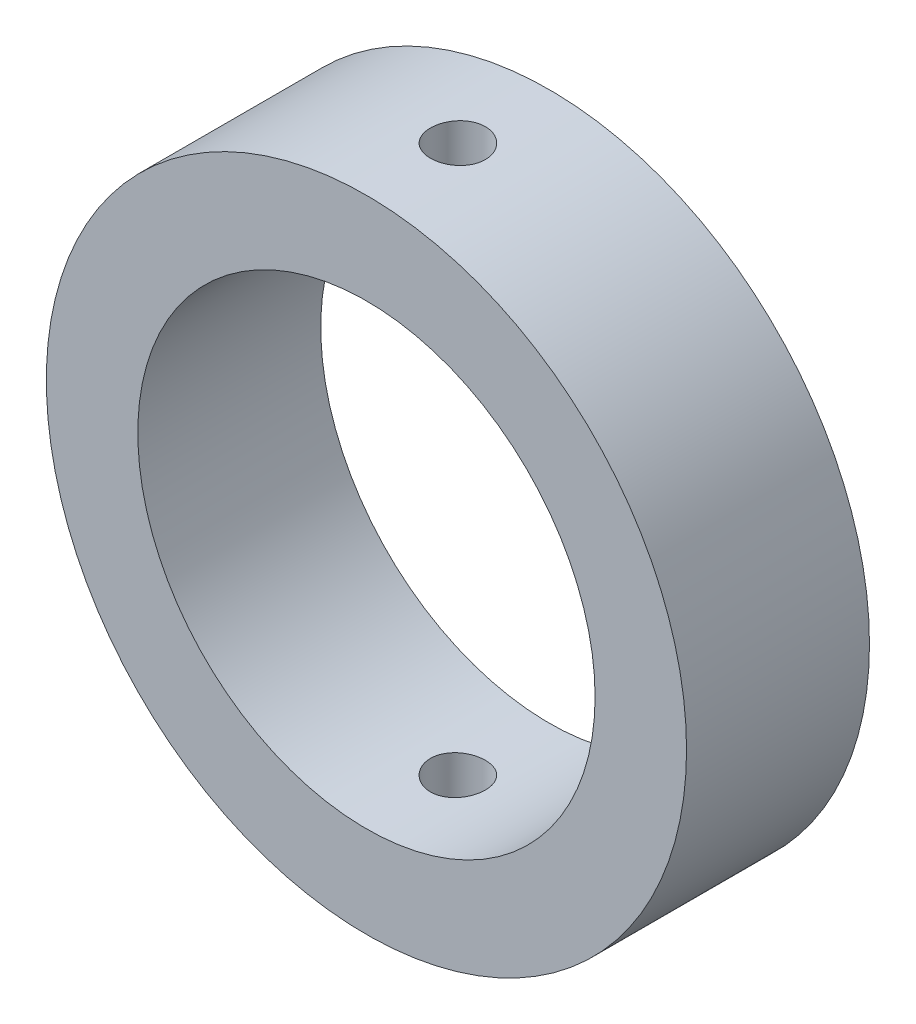
SolidWorks part; units mm, degrees
ref_plane "Front Plane" through (0, 0, 0) normal (0, 0, 1) x (1, 0, 0)
ref_plane "Top Plane" through (0, 0, 0) normal (0, 1, 0) x (1, 0, 0)
ref_plane "Right Plane" through (0, 0, 0) normal (1, 0, 0) x (0, 0, -1)
sketch "Sketch2" plane through (0, 0, 0) normal (0, 0, 1) x (1, 0, 0)
  circle A0 centre (0, 0) radius 250
  circle A1 centre (0, 0) radius 350
  dimension "D1" = 700
  dimension "D2" = 500
extrude "Boss-Extrude1" add sketch "Sketch2" along normal blind 200
sketch "Sketch3" plane through (0, 0, 0) normal (0, 1, 0) x (1, 0, 0)
  line L0 (350, 0) -> (-350, 0) construction
  circle A0 centre (0, -100) radius 30
  point P2 (0, 0)
  dimension "D1" = 60
  dimension "D2" = 100
extrude "Cut-Extrude1" cut sketch "Sketch3" against normal through all both and the other way through all
